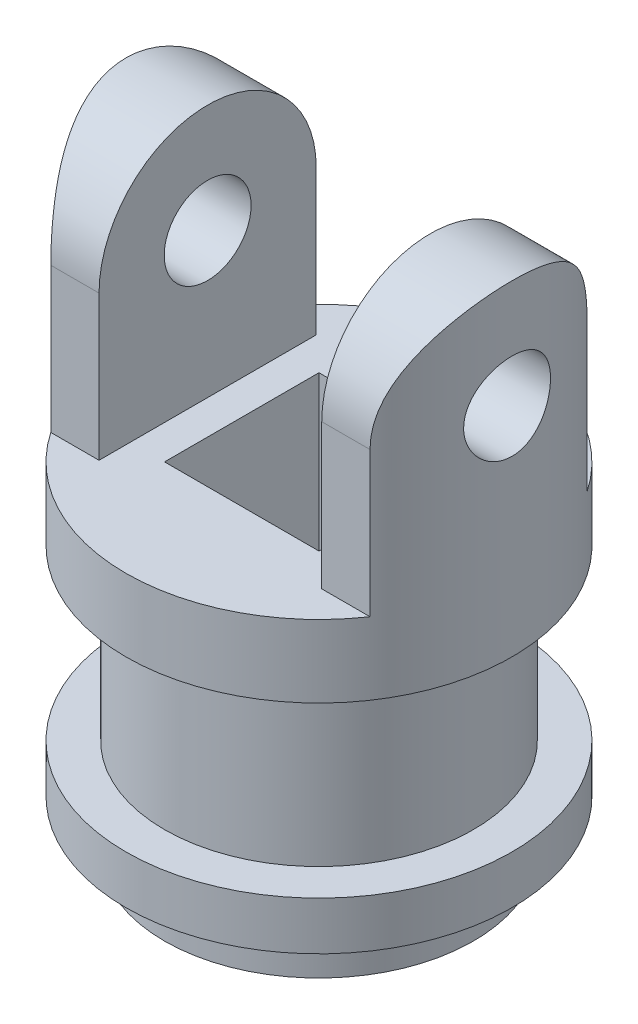
SolidWorks part; units mm, degrees
ref_plane "Ön Düzlem" through (0, 0, 0) normal (0, 0, 1) x (1, 0, 0)
ref_plane "Üst Düzlem" through (0, 0, 0) normal (0, 1, 0) x (1, 0, 0)
ref_plane "Sağ Düzlem" through (0, 0, 0) normal (1, 0, 0) x (0, 0, -1)
sketch "Çizim1" plane through (0, 0, 0) normal (0, 1, 0) x (1, 0, 0)
  circle A0 centre (0, 0) radius 32
  dimension "D1" = 64
extrude "Yükseklik-Ekstrüzyon1" add sketch "Çizim1" along normal blind 70
ref_plane "Düzlem1" through (0, 10, 0) normal (0, 1, 0) x (1, 0, 0)
sketch "Çizim2" plane through (0, 10, 0) normal (0, 1, 0) x (1, 0, 0)
  circle A0 centre (0, 0) radius 40
  dimension "D1" = 80
extrude "Yükseklik-Ekstrüzyon2" add sketch "Çizim2" along normal blind 10
ref_plane "Düzlem2" through (0, 55, 0) normal (0, 1, 0) x (1, 0, 0)
sketch "Çizim3" plane through (0, 55, 0) normal (0, 1, 0) x (1, 0, 0)
  circle A0 centre (0, 0) radius 40
  dimension "D1" = 80
extrude "Yükseklik-Ekstrüzyon3" add sketch "Çizim3" along normal blind 15
sketch "Çizim4" plane through (0, 70, 0) normal (0, 1, 0) x (1, 0, 0)
  line L0 (0, 0) -> (0, 12.7808) construction
  line L1 (0, 0) -> (-40, 0) construction
  line L11 (-16, 16) -> (16, 16)
  line L12 (-16, 16) -> (-16, -16)
  line L13 (-16, -16) -> (16, -16)
  line L14 (16, 16) -> (16, -16)
  line L15 (-16, 16) -> (16, -16) construction
  line L16 (-16, -16) -> (16, 16) construction
  circle A1 centre (0, 0) radius 40 construction
  point P10 (-13.0719, 0)
  dimension "D1" = 32
  dimension "D2" = 32
extrude "Kes-Ekstrüzyon1" cut sketch "Çizim4" against normal through all
sketch "Çizim5" plane through (0, 70, 0) normal (0, 1, 0) x (1, 0, 0)
  line L0 (0, 0) -> (-40, 0) construction
  line L1 (-23.0719, -22.5) -> (-23.0719, 22.5)
  line L2 (-23.0719, 22.5) -> (-33.0719, 22.5)
  line L3 (-23.0719, -22.5) -> (-33.0719, -22.5)
  line L4 (-33.0719, 22.5) -> (-33.0719, -22.5)
  line L5 (0, 0) -> (0, 8.1036) construction
  line L6 (23.0719, -22.5) -> (33.0719, -22.5)
  line L7 (33.0719, 22.5) -> (33.0719, -22.5)
  line L8 (23.0719, 22.5) -> (33.0719, 22.5)
  line L9 (23.0719, -22.5) -> (23.0719, 22.5)
  circle A0 centre (0, 0) radius 40 construction
  circle A1 centre (0, 0) radius 40
  point P9 (-23.0719, 0)
  circle M5 centre (0, 0) radius 40
  dimension "D3" = 80
  dimension "D1" = 45
  dimension "D2" = 10
extrude "Yükseklik-Ekstrüzyon6" add sketch "Çizim5" along normal blind 52.5 contours L2 L4 L3 L1 | L4 M5 | L9 L6 L7 L8 | L7 M5
ref_plane "Düzlem3" through (-40, 0, 0) normal (1, 0, 0) x (0, 0, -1)
sketch "Çizim7" [suppressed] plane through (-40, 0, 0) normal (1, 0, 0) x (0, 0, -1)
  line L0 (22.5, 122.5) -> (-22.5, 122.5) construction
  line L1 (-22.5, 122.5) -> (22.5, 122.5)
  line L2 (-22.5, 122.5) -> (-22.5, 70) construction
  line L3 (22.5, 122.5) -> (22.5, 70) construction
  circle A0 centre (0, 122.5) radius 9
  arc A1 (22.5, 122.5) -> (-22.5, 122.5) centre (0, 122.5) ccw
  dimension "D1" = 18
sketch "Çizim11" plane through (23.0719, 0, 0) normal (-1, 0, 0) x (0, 0, 1)
  line L0 (-22.5, 70) -> (-22.5, 100) construction
  line L1 (-22.5, 122.5) -> (-22.5, 70) construction
  line L2 (-22.5, 100) -> (22.5, 100) construction
  circle A0 centre (0, 100) radius 9
  arc A1 (22.5, 100) -> (-22.5, 100) centre (0, 100) ccw
  line M4 (22.5, 70) -> (22.5, 122.5)
  line M5 (22.5, 122.5) -> (-22.5, 122.5)
  line M6 (-22.5, 122.5) -> (-22.5, 70)
  dimension "D3" = 18
  dimension "D4" = 30
  dimension "D1" = 30
  dimension "D2" = 22.5
extrude "Kes-Ekstrüzyon2" cut sketch "Çizim11" against normal through all contours A0 | A1 M5 M6 | A1 M4 M5
sketch "Çizim12" plane through (-23.0719, 0, 0) normal (1, 0, 0) x (0, 0, -1)
  line L0 (-22.5, 100) -> (22.5, 100) construction
  circle A0 centre (0, 100) radius 9
  arc A1 (22.5, 100) -> (-22.5, 100) centre (0, 100) ccw
  line M2 (22.5, 70) -> (22.5, 122.5)
  line M3 (22.5, 122.5) -> (-22.5, 122.5)
  line M4 (-22.5, 122.5) -> (-22.5, 70)
  dimension "D2" = 18
extrude "Kes-Ekstrüzyon3" cut sketch "Çizim12" against normal through all contours A1 M3 M4 | A0 L0 | L0 A0 | A1 M2 M3
